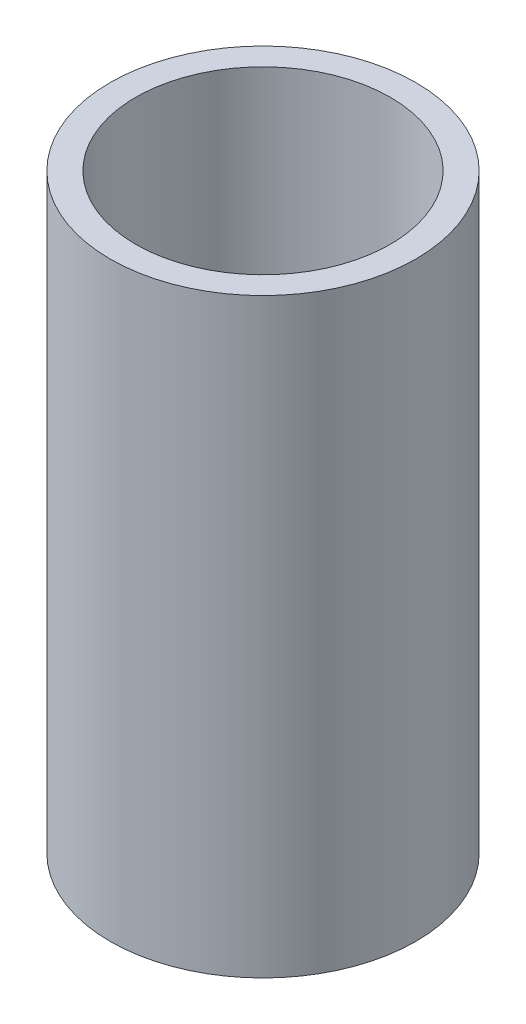
SolidWorks part; units mm, degrees
ref_plane "Alzado" through (0, 0, 0) normal (0, 0, 1) x (1, 0, 0)
ref_plane "Planta" through (0, 0, 0) normal (0, 1, 0) x (1, 0, 0)
ref_plane "Vista lateral" through (0, 0, 0) normal (1, 0, 0) x (0, 0, -1)
sketch "Croquis1" plane through (0, 0, 0) normal (0, 0, 1) x (1, 0, 0)
  line L0 (0, 0) -> (0, 203) construction
  line L1 (-43.75, 203) -> (-52.5, 203)
  line L2 (-52.5, 203) -> (-52.5, 0)
  line L3 (-52.5, 0) -> (-43.75, 0)
  line L4 (-43.75, 0) -> (-43.75, 203)
  dimension "D1" = 203
  dimension "D2" = 52.5
  dimension "D3" = 8.75
revolve "Revolución1" add sketch "Croquis1" angle 360 about L0
